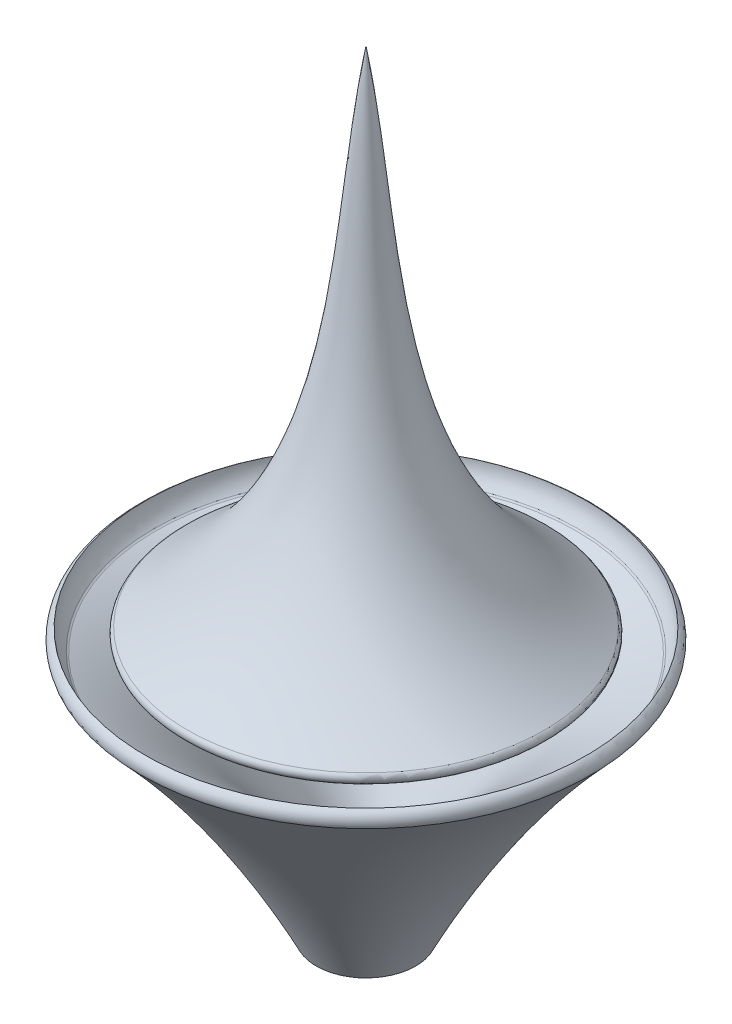
SolidWorks part; units mm, degrees
ref_plane "Front Plane" through (0, 0, 0) normal (0, 0, 1) x (1, 0, 0)
ref_plane "Top Plane" through (0, 0, 0) normal (0, 1, 0) x (1, 0, 0)
ref_plane "Right Plane" through (0, 0, 0) normal (1, 0, 0) x (0, 0, -1)
sketch "Sketch1" plane through (0, 0, 0) normal (0, 0, 1) x (1, 0, 0)
  line L0 (0, 0) -> (0, 88.2021) construction
  line L1 (-33.4622, 0) -> (0, 0)
  line L2 (0, 0) -> (0, 88.2021)
  spline S0 degree 3 poles (0, 88.2021) (-5.4067, 57.5987) (-1.6797, 19.1948) (-33.4622, 0) knots 0 0 0 0 1 1 1 1
revolve "Revolve1" add sketch "Sketch1" angle 360 about L0
sketch "Sketch2" plane through (0, 0, 0) normal (0, 0, 1) x (1, 0, 0)
  line L0 (-8.5346, -44.2877) -> (-3.524, -44.2877)
  line L1 (-3.524, -35.9249) -> (-3.524, -44.2877)
  arc A0 (-37.8596, 1.6855) -> (-38.6527, -0.809) centre (-36.8777, 0) ccw
  spline S0 degree 3 poles (-36.2496, -1.8468) (-23.7439, -7.8205) (-12.014, -19.8597) (-4.4433, -34.037) (-3.524, -35.9249) knots 0 0 0 0 0.729676 0.839931 0.839931 0.839931 0.839931
  spline S1 degree 2 poles (-36.2496, -1.8468) (-37.7727, -0.3854) (-37.8596, 1.6855) knots 0 0 0 1 1 1
  spline S2 degree 2 poles (-38.6527, -0.809) (-20.408, -20.206) (-8.5346, -44.2877) knots 0 0 0 1 1 1
sketch "Sketch3" plane through (0, 0, 0) normal (0, 0, 1) x (1, 0, 0)
  line L0 (0, 0) -> (0, 93.0096) construction
revolve "Revolve3" add sketch "Sketch2" angle 360 about L0
fillet "Fillet2" radius 1 3 edges at (0, -44.2877, -3.524) (0, -35.9249, -3.524) (0, -1.8468, -36.2496)
fillet "Fillet3" radius 1 1 edges at (0, 0, -33.4622)
